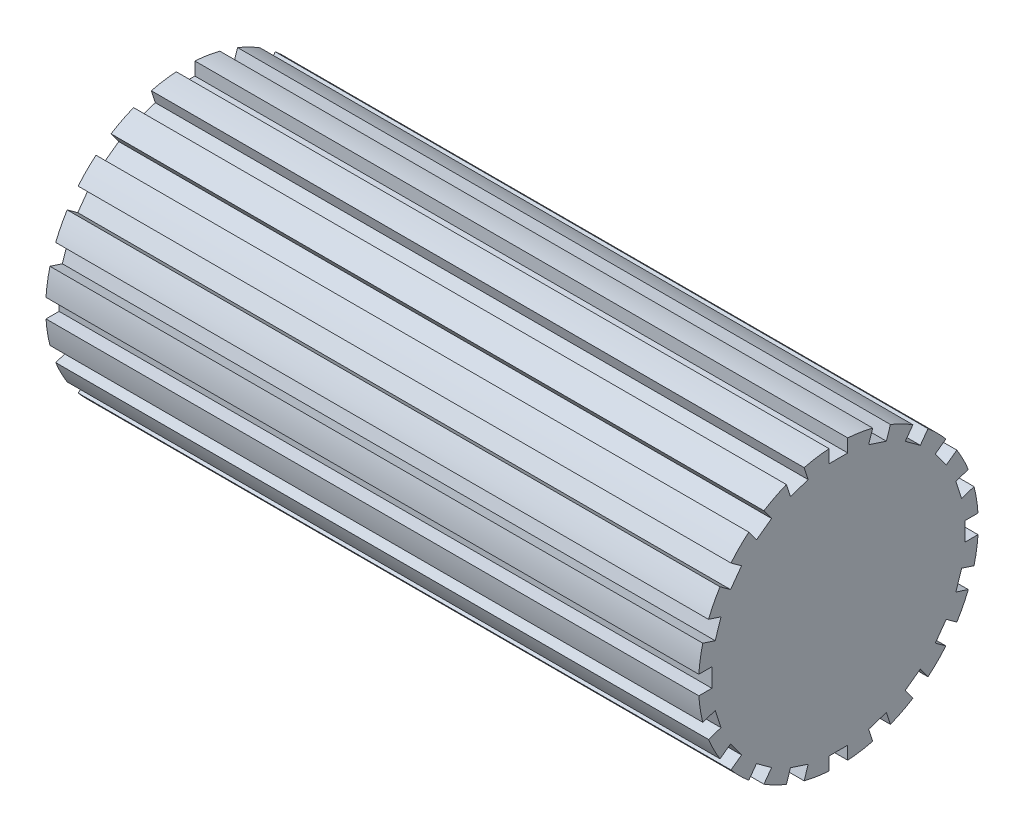
SolidWorks part; units mm, degrees
ref_plane "Front Plane" through (0, 0, 0) normal (0, 0, 1) x (1, 0, 0)
ref_plane "Top Plane" through (0, 0, 0) normal (0, 1, 0) x (1, 0, 0)
ref_plane "Right Plane" through (0, 0, 0) normal (1, 0, 0) x (0, 0, -1)
sketch "Sketch1" plane through (0, 0, 0) normal (0, 1, 0) x (1, 0, 0)
  line L0 (17.67, 0) -> (-26.3164, 0) construction
  line L1 (-22.225, 0) -> (-22.225, 9.525)
  line L2 (-22.225, 9.525) -> (22.225, 9.525)
  line L3 (22.225, 9.525) -> (22.225, 0)
  line L4 (-22.225, 0) -> (22.225, 0)
  point P5 (0, 9.525)
  dimension "D1" = 9.525
  dimension "D2" = 44.45
revolve "Revolve1" add sketch "Sketch1" angle 360 about L0
sketch "Sketch2" plane through (22.225, 0, 0) normal (1, 0, 0) x (0, 0, -1)
  line L0 (0, 0) -> (0, 9.9724) construction
  line L1 (-0.635, 8.6148) -> (0.635, 8.6148)
  line L2 (0.635, 8.6148) -> (0.635, 9.5038)
  line L3 (-0.635, 8.6148) -> (-0.635, 9.5038)
  line L4 (2.0582, 8.3894) -> (2.3329, 9.2349)
  line L5 (2.0582, 8.3894) -> (3.266, 7.9969)
  line L6 (3.266, 7.9969) -> (3.5408, 8.8424)
  line L7 (4.5499, 7.3428) -> (5.0725, 8.062)
  line L8 (4.5499, 7.3428) -> (5.5774, 6.5963)
  line L9 (5.5774, 6.5963) -> (6.0999, 7.3155)
  line L10 (6.5963, 5.5774) -> (7.3155, 6.0999)
  line L11 (6.5963, 5.5774) -> (7.3428, 4.5499)
  line L12 (7.3428, 4.5499) -> (8.062, 5.0725)
  line L13 (7.9969, 3.266) -> (8.8424, 3.5408)
  line L14 (7.9969, 3.266) -> (8.3894, 2.0582)
  line L15 (8.3894, 2.0582) -> (9.2349, 2.3329)
  line L16 (8.6148, 0.635) -> (9.5038, 0.635)
  line L17 (8.6148, 0.635) -> (8.6148, -0.635)
  line L18 (8.6148, -0.635) -> (9.5038, -0.635)
  line L19 (8.3894, -2.0582) -> (9.2349, -2.3329)
  line L20 (8.3894, -2.0582) -> (7.9969, -3.266)
  line L21 (7.9969, -3.266) -> (8.8424, -3.5408)
  line L22 (7.3428, -4.5499) -> (8.062, -5.0725)
  line L23 (7.3428, -4.5499) -> (6.5963, -5.5774)
  line L24 (6.5963, -5.5774) -> (7.3155, -6.0999)
  line L25 (5.5774, -6.5963) -> (6.0999, -7.3155)
  line L26 (5.5774, -6.5963) -> (4.5499, -7.3428)
  line L27 (4.5499, -7.3428) -> (5.0725, -8.062)
  line L28 (3.266, -7.9969) -> (3.5408, -8.8424)
  line L29 (3.266, -7.9969) -> (2.0582, -8.3894)
  line L30 (2.0582, -8.3894) -> (2.3329, -9.2349)
  line L31 (0.635, -8.6148) -> (0.635, -9.5038)
  line L32 (0.635, -8.6148) -> (-0.635, -8.6148)
  line L33 (-0.635, -8.6148) -> (-0.635, -9.5038)
  line L34 (-2.0582, -8.3894) -> (-2.3329, -9.2349)
  line L35 (-2.0582, -8.3894) -> (-3.266, -7.9969)
  line L36 (-3.266, -7.9969) -> (-3.5408, -8.8424)
  line L37 (-4.5499, -7.3428) -> (-5.0725, -8.062)
  line L38 (-4.5499, -7.3428) -> (-5.5774, -6.5963)
  line L39 (-5.5774, -6.5963) -> (-6.0999, -7.3155)
  line L40 (-6.5963, -5.5774) -> (-7.3155, -6.0999)
  line L41 (-6.5963, -5.5774) -> (-7.3428, -4.5499)
  line L42 (-7.3428, -4.5499) -> (-8.062, -5.0725)
  line L43 (-7.9969, -3.266) -> (-8.8424, -3.5408)
  line L44 (-7.9969, -3.266) -> (-8.3894, -2.0582)
  line L45 (-8.3894, -2.0582) -> (-9.2349, -2.3329)
  line L46 (-8.6148, -0.635) -> (-9.5038, -0.635)
  line L47 (-8.6148, -0.635) -> (-8.6148, 0.635)
  line L48 (-8.6148, 0.635) -> (-9.5038, 0.635)
  line L49 (-8.3894, 2.0582) -> (-9.2349, 2.3329)
  line L50 (-8.3894, 2.0582) -> (-7.9969, 3.266)
  line L51 (-7.9969, 3.266) -> (-8.8424, 3.5408)
  line L52 (-7.3428, 4.5499) -> (-8.062, 5.0725)
  line L53 (-7.3428, 4.5499) -> (-6.5963, 5.5774)
  line L54 (-6.5963, 5.5774) -> (-7.3155, 6.0999)
  line L55 (-5.5774, 6.5963) -> (-6.0999, 7.3155)
  line L56 (-5.5774, 6.5963) -> (-4.5499, 7.3428)
  line L57 (-4.5499, 7.3428) -> (-5.0725, 8.062)
  line L58 (-3.266, 7.9969) -> (-3.5408, 8.8424)
  line L59 (-3.266, 7.9969) -> (-2.0582, 8.3894)
  line L60 (-2.0582, 8.3894) -> (-2.3329, 9.2349)
  circle A0 centre (0, 0) radius 9.525 construction
  arc A1 (-3.5408, 8.8424) -> (-5.0725, 8.062) centre (0, 0) ccw
  arc A2 (-6.0999, 7.3155) -> (-7.3155, 6.0999) centre (0, 0) ccw
  arc A3 (-8.062, 5.0725) -> (-8.8424, 3.5408) centre (0, 0) ccw
  arc A4 (-9.2349, 2.3329) -> (-9.5038, 0.635) centre (0, 0) ccw
  arc A5 (-9.5038, -0.635) -> (-9.2349, -2.3329) centre (0, 0) ccw
  arc A6 (-8.8424, -3.5408) -> (-8.062, -5.0725) centre (0, 0) ccw
  arc A7 (-7.3155, -6.0999) -> (-6.0999, -7.3155) centre (0, 0) ccw
  arc A8 (-5.0725, -8.062) -> (-3.5408, -8.8424) centre (0, 0) ccw
  arc A9 (-2.3329, -9.2349) -> (-0.635, -9.5038) centre (0, 0) ccw
  arc A10 (0.635, -9.5038) -> (2.3329, -9.2349) centre (0, 0) ccw
  arc A11 (3.5408, -8.8424) -> (5.0725, -8.062) centre (0, 0) ccw
  arc A12 (6.0999, -7.3155) -> (7.3155, -6.0999) centre (0, 0) ccw
  arc A13 (8.062, -5.0725) -> (8.8424, -3.5408) centre (0, 0) ccw
  arc A14 (9.2349, -2.3329) -> (9.5038, -0.635) centre (0, 0) ccw
  arc A15 (9.5038, 0.635) -> (9.2349, 2.3329) centre (0, 0) ccw
  arc A16 (8.8424, 3.5408) -> (8.062, 5.0725) centre (0, 0) ccw
  arc A17 (7.3155, 6.0999) -> (6.0999, 7.3155) centre (0, 0) ccw
  arc A18 (5.0725, 8.062) -> (3.5408, 8.8424) centre (0, 0) ccw
  arc A19 (2.3329, 9.2349) -> (0.635, 9.5038) centre (0, 0) ccw
  arc A20 (-0.635, 9.5038) -> (-2.3329, 9.2349) centre (0, 0) ccw
  point P10 (0, 8.6148)
  dimension "D1" = 0.635
  dimension "D2" = 0.889
  dimension "D3" = 20
extrude "Cut-Extrude1" cut sketch "Sketch2" against normal up to next (44.45 mm away) flip side to cut
